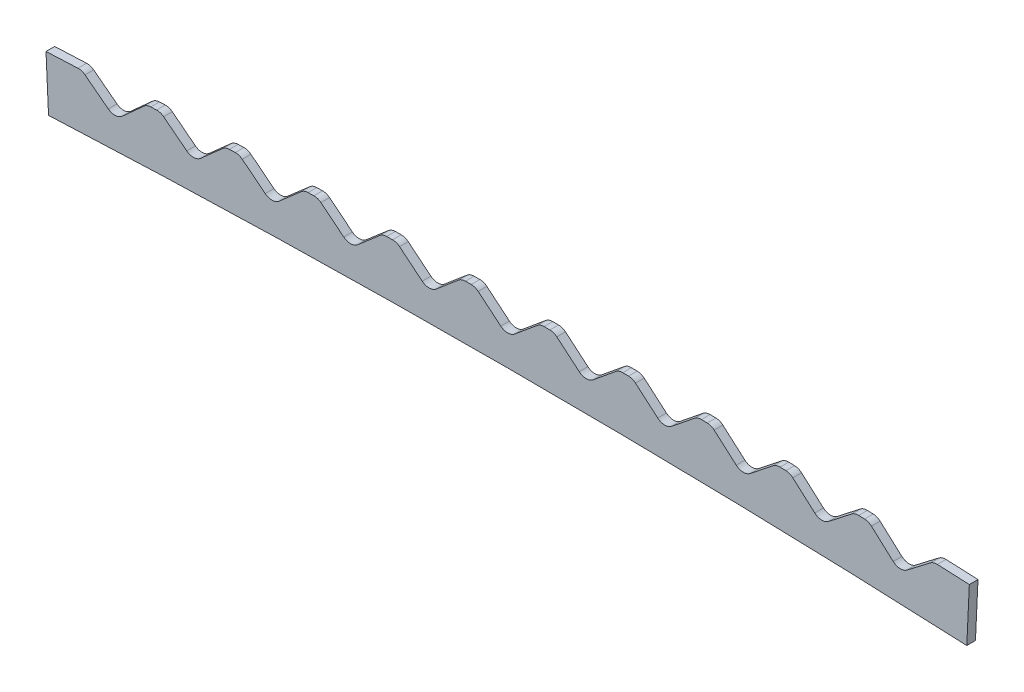
SolidWorks part; units mm, degrees
ref_plane "Plan de face" through (0, 0, 0) normal (0, 0, 1) x (1, 0, 0)
ref_plane "Plan de dessus" through (0, 0, 0) normal (0, 1, 0) x (1, 0, 0)
ref_plane "Plan de droite" through (0, 0, 0) normal (1, 0, 0) x (0, 0, -1)
sketch "Esquisse1" plane through (0, 0, 0) normal (0, 0, 1) x (1, 0, 0)
  line L0 (0, 0) -> (0, 2581.6249) construction
  line L1 (0, -9000) -> (-517.1978, 1967.1527) construction
  line L2 (0, -9000) -> (614.0831, 4021.6014) construction
  line L3 (423.9581, -9.9911) -> (426.3134, 39.9534)
  line L4 (-423.9581, -9.9911) -> (-426.3134, 39.9534)
  arc A0 (-423.9581, -9.9911) -> (423.9581, -9.9911) centre (0, -9000) cw
  arc A1 (-426.3134, 39.9534) -> (426.3134, 39.9534) centre (0, -9000) cw
  point P3 (0, 0)
  point P8 (0, 50)
  point P46 (0, -16000)
  point P60 (-0.6877, -10183.3172)
  point P110 (0, -10000)
  dimension "D1" = 9000
  dimension "D3" = 50
  dimension "D4" = 848.23
  dimension "D2" = 5.4
  dimension "D5" = 847.9161
extrude "Boss.-Extru.2" add sketch "Esquisse1" along normal blind 8
sketch "Esquisse2" plane through (0, 0, 8) normal (0, 0, 1) x (1, 0, 0)
  line L0 (0, 25) -> (30, 49.9503)
  line L2 (30, 49.9503) -> (0, 74.9953)
  line L3 (0, 74.9953) -> (-30, 49.9503)
  line L4 (-30, 49.9503) -> (0, 25)
  line L5 (0, 0) -> (0, 50) construction
  arc A1 (426.3134, 39.9534) -> (-426.3134, 39.9534) centre (0, -9000) ccw construction
  arc A2 (426.3134, 39.9534) -> (-426.3134, 39.9534) centre (0, -9000) ccw construction
  point P5 (0, 50)
  dimension "D1" = 25
  dimension "D2" = 30
  dimension "D3" = 49.9953
extrude "Enlèv. mat.-Extru.1" cut sketch "Esquisse2" against normal through all
fillet "Congé1" radius 10 3 edges at (30, 49.9503, 4) (-30, 49.9503, 4) (0, 25, 4)
pattern_circular "Répétition circulaire1" count 6 every 0.46 about axis through (0, -9000, 0) along (0, 0, 1) of "Congé1", "Enlèv. mat.-Extru.1"
pattern_circular "Répétition circulaire2" count 6 every 0.46 about axis through (0, -9000, 0) along (0, 0, 1) of "Congé1", "Enlèv. mat.-Extru.1"
ref_plane "Plan1" through (-418.8603, -19.753, 44.0729) normal (-0.9934, -0.0468, 0.1045) x (0.0471, -0.9989, 0)
